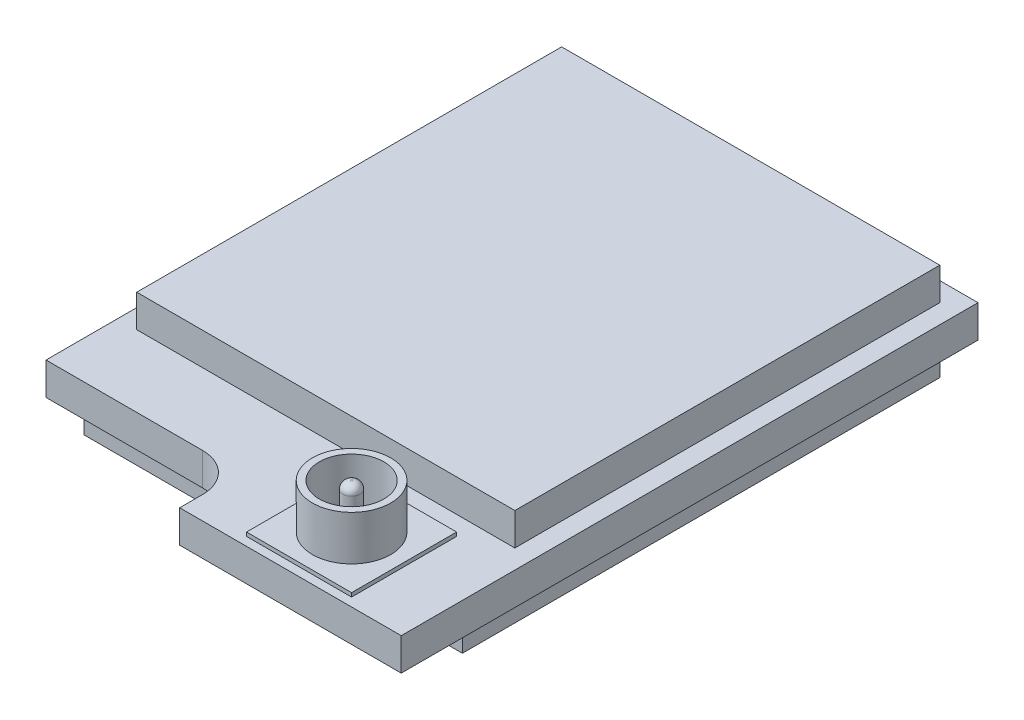
SolidWorks part; units mm, degrees
ref_plane "Front Plane" through (0, 0, 0) normal (0, 0, 1) x (1, 0, 0)
ref_plane "Top Plane" through (0, 0, 0) normal (0, 1, 0) x (1, 0, 0)
ref_plane "Right Plane" through (0, 0, 0) normal (1, 0, 0) x (0, 0, -1)
sketch "Sketch1" plane through (0, 0, 0) normal (0, 1, 0) x (1, 0, 0)
  line L0 (-5.45, -6.75) -> (-1.35, -6.75)
  line L2 (5.45, -6.75) -> (5.45, 6.75)
  line L3 (5.45, 6.75) -> (-5.45, 6.75)
  line L4 (-5.45, -6.75) -> (-5.45, 6.75)
  line L5 (5.45, -6.75) -> (-5.45, 6.75) construction
  line L6 (5.45, 6.75) -> (-5.45, -6.75) construction
  line L7 (-0.35, -7.75) -> (-0.35, -8.35)
  line L8 (-0.35, -8.35) -> (5.45, -8.35)
  line L9 (5.45, -8.35) -> (5.45, -6.75)
  arc A0 (-1.35, -6.75) -> (-0.35, -7.75) centre (-1.35, -7.75) cw
  point P0 (0, 0)
  dimension "D5" = 1
  dimension "D1" = 10.9
  dimension "D2" = 15.1
  dimension "D3" = 13.5
  dimension "D4" = 5.8
extrude "Boss-Extrude1" add sketch "Sketch1" along normal mid plane 0.85
sketch "Sketch2" plane through (0, 0.425, 0) normal (0, 1, 0) x (1, 0, 0)
  line L0 (1.175, -8.125) -> (3.925, -5.375) construction
  line L1 (1.175, -5.375) -> (3.925, -5.375)
  line L2 (1.175, -5.375) -> (1.175, -8.125)
  line L3 (1.175, -8.125) -> (3.925, -8.125)
  line L4 (3.925, -5.375) -> (3.925, -8.125)
  line L5 (-5.45, -6.75) -> (-1.35, -6.75) construction
  line L6 (-0.35, -8.35) -> (5.45, -8.35) construction
  point P2 (2.55, -6.75)
  point P10 (2.55, -8.35)
  dimension "D1" = 2.75
extrude "Boss-Extrude2" add sketch "Sketch2" along normal blind 0.1
sketch "Sketch3" plane through (0, 0.525, 0) normal (0, 1, 0) x (1, 0, 0)
  line L0 (1.175, -5.375) -> (3.925, -8.125) construction
  line L1 (1.175, -5.375) -> (1.175, -8.125) construction
  line L2 (3.925, -5.375) -> (1.175, -5.375) construction
  circle A0 centre (2.55, -6.75) radius 0.845
  circle A1 centre (2.55, -6.75) radius 1.025
  circle A2 centre (2.55, -6.75) radius 0.225
  point P3 (1.525, -6.75)
  point P7 (2.55, -6.75)
  point P13 (1.705, -6.75)
  dimension "D1" = 2.05
  dimension "D3" = 0.45
  dimension "D2" = 0.18
extrude "Boss-Extrude3" add sketch "Sketch3" along normal blind 2.12 from surface at -0.95 contours A1 L0 A0 | L0 A1 A0 | L0 A2 | A2 L0 starting at face at (-0.2633, -0.425, 3.4633)
fillet "Fillet1" radius 0.2 1 edges at (2.55, 1.695, 6.525)
sketch "Sketch4" plane through (0, -0.425, 0) normal (0, -1, 0) x (1, 0, 0)
  line L0 (5.45, -6.25) -> (4.95, -6.25) construction
  line L1 (-4.95, 6.25) -> (4.95, 6.25)
  line L2 (-4.95, 6.25) -> (-4.95, -6.25)
  line L3 (-4.95, -6.25) -> (4.95, -6.25)
  line L4 (4.95, 6.25) -> (4.95, -6.25)
  line L5 (-4.95, 6.25) -> (4.95, -6.25) construction
  line L6 (-4.95, -6.25) -> (4.95, 6.25) construction
  line L7 (5.45, 8.35) -> (5.45, -6.75) construction
  line L8 (4.95, -6.25) -> (4.95, -6.75) construction
  line L9 (5.45, -6.75) -> (-5.45, -6.75) construction
  point P0 (0, 0)
  dimension "D1" = 0.5
extrude "Boss-Extrude4" add sketch "Sketch4" along normal blind 1.7 from surface at -0.85 starting at face at (-0.2633, 0.425, 3.4633)
sketch "Sketch5" plane through (0, 0.425, 0) normal (0, 1, 0) x (1, 0, 0)
  line L0 (-4.95, 6.75) -> (-4.95, 6.25) construction
  line L1 (-4.95, 6.25) -> (4.95, 6.25)
  line L2 (-4.95, 6.25) -> (-4.95, -4.875)
  line L3 (-4.95, -4.875) -> (4.95, -4.875)
  line L4 (4.95, 6.25) -> (4.95, -4.875)
  line L5 (5.45, 6.75) -> (-5.45, 6.75) construction
  line L6 (-5.45, 6.25) -> (-4.95, 6.25) construction
  line L7 (-5.45, 6.75) -> (-5.45, -6.75) construction
  line L8 (3.925, -5.375) -> (1.175, -5.375) construction
  point P12 (0, 6.25)
  dimension "D1" = 0.5
  dimension "D2" = 0.5
extrude "Boss-Extrude5" add sketch "Sketch5" along normal blind 1.7 from surface at -0.85 starting at face at (-0.2633, -0.425, 3.4633)
